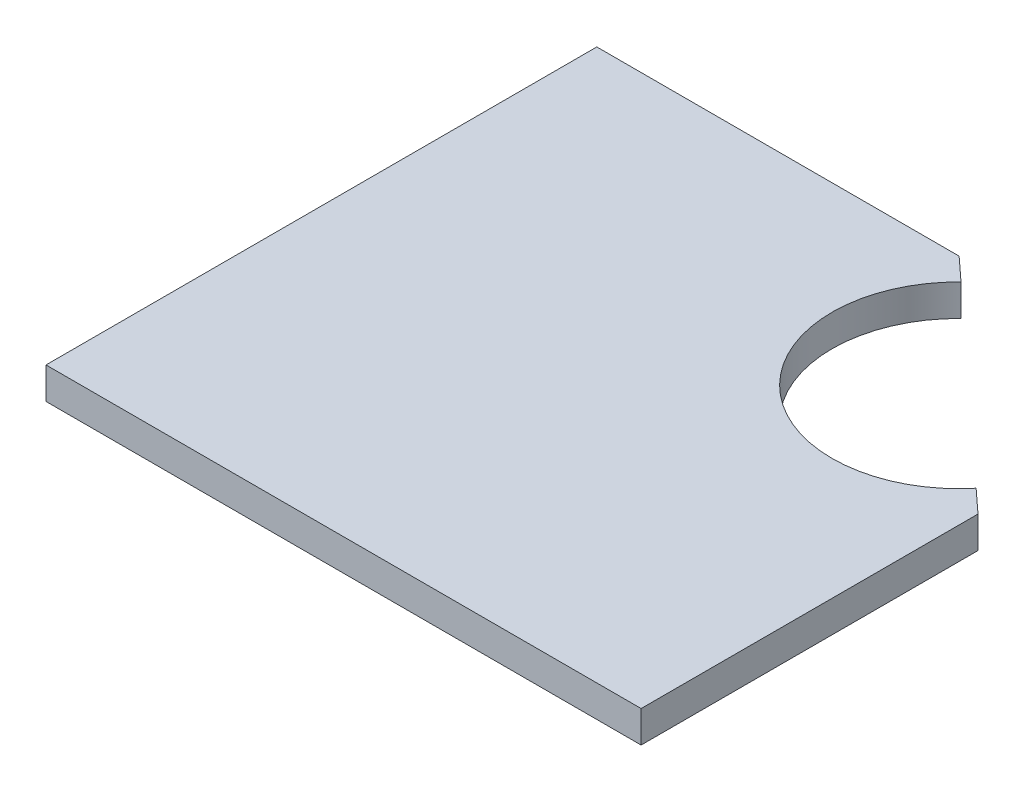
SolidWorks part; units mm, degrees
ref_plane "Face" through (0, 0, 0) normal (0, 0, 1) x (1, 0, 0)
ref_plane "Dessus" through (0, 0, 0) normal (0, 1, 0) x (1, 0, 0)
ref_plane "Droite" through (0, 0, 0) normal (1, 0, 0) x (0, 0, -1)
sketch "Esquisse1" plane through (0, 0, 0) normal (0, 1, 0) x (1, 0, 0)
  line L0 (-47, 43.5) -> (10.2285, 43.5)
  line L1 (47, -43.5) -> (-47, -43.5)
  line L2 (47, -43.5) -> (47, 43.5) construction
  line L3 (47, 43.5) -> (-47, 43.5) construction
  line L4 (-47, -43.5) -> (-47, 43.5)
  line L5 (47, -43.5) -> (-47, 43.5) construction
  line L6 (47, 43.5) -> (-47, -43.5) construction
  line L8 (47, 9.7106) -> (47, -43.5)
  line L10 (10.2285, 43.5) -> (13.9101, 40.1169)
  line L11 (43.3183, 13.0937) -> (47, 9.7106)
  arc A0 (13.9101, 40.1169) -> (43.3183, 13.0937) centre (27.8649, 25.7899) ccw
  point P0 (0, 0)
  point P10 (14.3326, 11.0632)
  dimension "D1" = 87
  dimension "D3" = 40
  dimension "D4" = 69.2899
  dimension "D2" = 94
  dimension "D5" = 5
extrude "Boss.-Extru.1" add sketch "Esquisse1" along normal blind 5
sketch "Esquisse2" plane through (0, 5, 0) normal (0, 1, 0) x (1, 0, 0)
  arc A0 (13.9101, 40.1169) -> (43.3183, 13.0937) centre (27.8649, 25.7899) ccw construction
  point P0 (14.3326, 11.0632)
